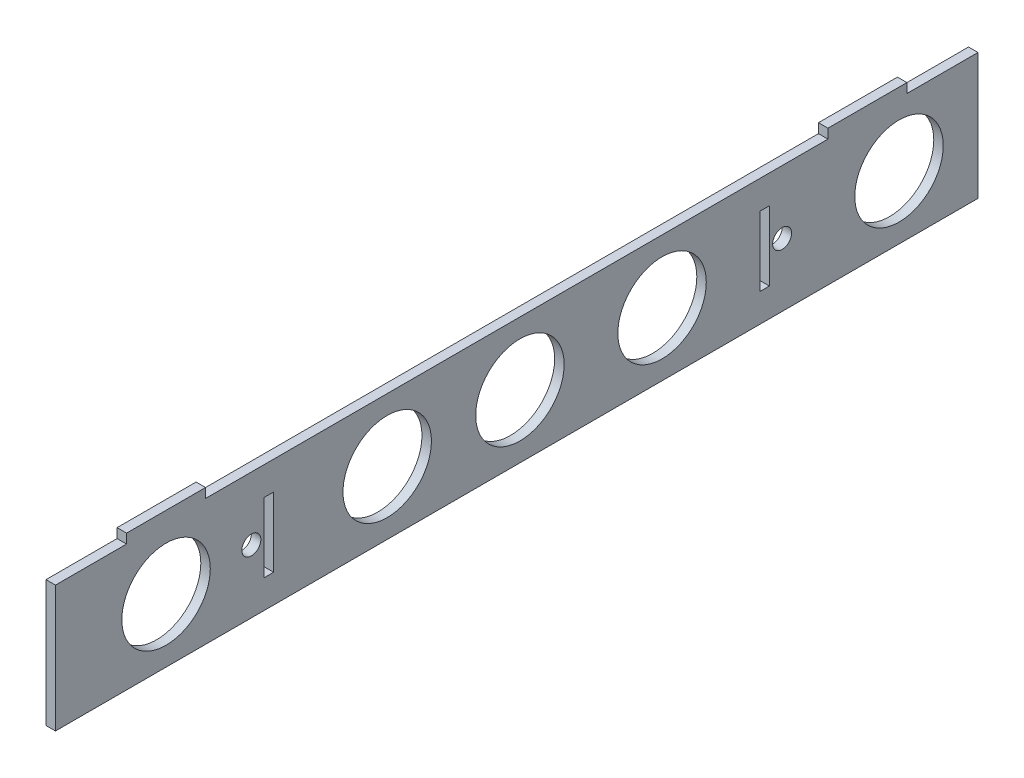
SolidWorks part; units mm, degrees
ref_plane "Front Plane" through (0, 0, 0) normal (0, 0, 1) x (1, 0, 0)
ref_plane "Top Plane" through (0, 0, 0) normal (0, 1, 0) x (1, 0, 0)
ref_plane "Right Plane" through (0, 0, 0) normal (1, 0, 0) x (0, 0, -1)
sketch "Sketch3" plane through (0, 0, 0) normal (1, 0, 0) x (0, 0, -1)
  line L1 (0, 0) -> (292, 0)
  line L2 (0, 0) -> (0, -40)
  line L3 (0, -40) -> (292, -40)
  line L4 (292, 0) -> (292, -40)
  line L5 (22.5, 0) -> (47.5, 0)
  line L6 (22.5, 0) -> (22.5, 3)
  line L7 (22.5, 3) -> (47.5, 3)
  line L8 (47.5, 0) -> (47.5, 3)
  line L9 (244.5, 0) -> (269.5, 0)
  line L10 (244.5, 0) -> (244.5, 3)
  line L11 (244.5, 3) -> (269.5, 3)
  line L12 (269.5, 0) -> (269.5, 3)
  line L13 (0, -9) -> (3, -9) construction
  line L14 (0, -9) -> (0, -31) construction
  line L15 (0, -31) -> (3, -31) construction
  line L16 (3, -9) -> (3, -31) construction
  line L17 (292, -9) -> (289, -9) construction
  line L18 (292, -9) -> (292, -31) construction
  line L19 (292, -31) -> (289, -31) construction
  line L20 (289, -9) -> (289, -31) construction
  line L21 (66.04, -9) -> (69.04, -9)
  line L22 (66.04, -9) -> (66.04, -31)
  line L23 (66.04, -31) -> (69.04, -31)
  line L24 (69.04, -9) -> (69.04, -31)
  line L25 (222.96, -9) -> (225.96, -9)
  line L26 (222.96, -9) -> (222.96, -31)
  line L27 (222.96, -31) -> (225.96, -31)
  line L28 (225.96, -9) -> (225.96, -31)
  point P29 (67.54, -9)
  point P30 (224.46, -9)
  point P32 (3, -20)
  point P33 (69.04, -20)
  point P34 (225.96, -20)
  point P35 (289, -20)
  point P36 (292, -20)
  point P37 (66.04, -20)
  point P38 (35, 3)
  point P39 (257, 3)
  dimension "D1" = 40
  dimension "D2" = 292
  dimension "D3" = 67.54
  dimension "D4" = 67.54
  dimension "D5" = 25
  dimension "D6" = 25
  dimension "D7" = 3
  dimension "D8" = 22
  dimension "D9" = 22
  dimension "D10" = 22
  dimension "D11" = 22
  dimension "D12" = 35
  dimension "D13" = 35
extrude "Boss-Extrude2" add sketch "Sketch3" along normal blind 3 contours L20 L17 L4 L1 L2 L13 L16 L15 L3 L19 L21 L24 L23 L22 L25 L28 L27 L26 | L1 L8 L7 L6 | L1 L12 L11 L10
sketch "Sketch5" plane through (3, 0, 0) normal (1, 0, 0) x (0, 0, -1)
  line L0 (0, -20) -> (292, -20) construction
  line L1 (0, 0) -> (0, -40) construction
  line L2 (292, 0) -> (292, -40) construction
  circle A0 centre (35, -20) radius 14
  circle A1 centre (105, -20) radius 14
  circle A2 centre (147, -20) radius 14
  circle A3 centre (192, -20) radius 14
  circle A4 centre (267, -20) radius 14
  dimension "D1" = 28
  dimension "D2" = 35
  dimension "D3" = 105
  dimension "D4" = 100
  dimension "D5" = 25
  dimension "D6" = 147
extrude "Cut-Extrude1" cut sketch "Sketch5" against normal blind 10
sketch "Sketch6" plane through (3, 0, 0) normal (1, 0, 0) x (0, 0, -1)
  line L0 (0, -20) -> (292, -20) construction
  line L1 (0, 0) -> (0, -40) construction
  line L2 (292, 0) -> (292, -40) construction
  circle A0 centre (62, -20) radius 3
  circle A1 centre (230, -20) radius 3
  dimension "D1" = 6
  dimension "D4" = 6
  dimension "D2" = 62
  dimension "D3" = 62
extrude "Cut-Extrude2" cut sketch "Sketch6" against normal blind 10
